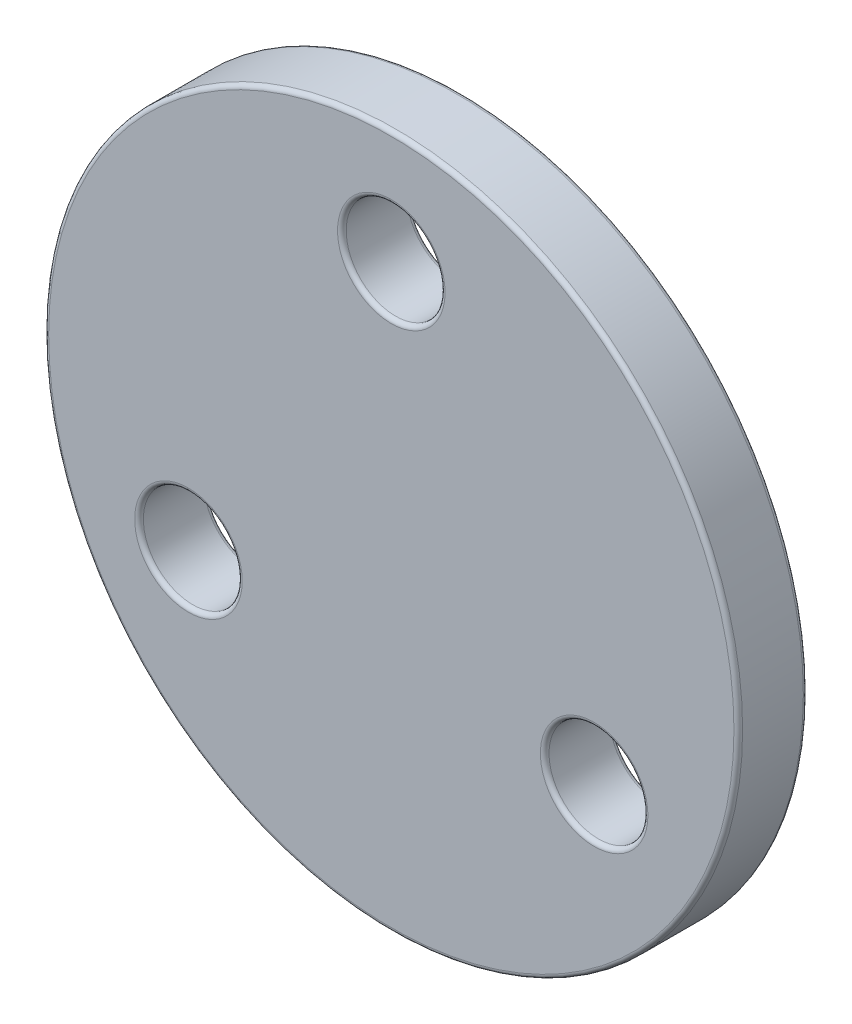
SolidWorks part; units mm, degrees
ref_plane "Alzado" through (0, 0, 0) normal (0, 0, 1) x (1, 0, 0)
ref_plane "Planta" through (0, 0, 0) normal (0, 1, 0) x (1, 0, 0)
ref_plane "Vista lateral" through (0, 0, 0) normal (1, 0, 0) x (0, 0, -1)
sketch "Croquis1" plane through (0, 0, 0) normal (0, 0, 1) x (1, 0, 0)
  circle A0 centre (0, 0) radius 20
  dimension "D1" = 40
extrude "Saliente-Extruir1" add sketch "Croquis1" along normal blind 4
sketch "Croquis2" plane through (0, 0, 0) normal (0, 0, 1) x (1, 0, 0)
  circle A0 centre (0, 0) radius 13.5
  circle A1 centre (0, 13.5) radius 2.85
  circle A2 centre (11.6913, -6.75) radius 2.85
  circle A3 centre (-11.6913, -6.75) radius 2.85
  point P11 (0, 0)
  dimension "D1" = 27
  dimension "D2" = 5.7
  dimension "D3" = 3
extrude "Cortar-Extruir2" cut sketch "Croquis2" along normal up to surface (4 mm away) contours A0 A1 | A0 A1 | A3 | A2
fillet "Redondeo1" radius 0.25 8 edges at (14.5413, -6.75, 4) (14.5413, -6.75, 0) (-8.8413, -6.75, 4) (-8.8413, -6.75, 0) (2.85, 13.5, 4) (2.85, 13.5, 0) (20, 0, 4) (20, 0, 0)
